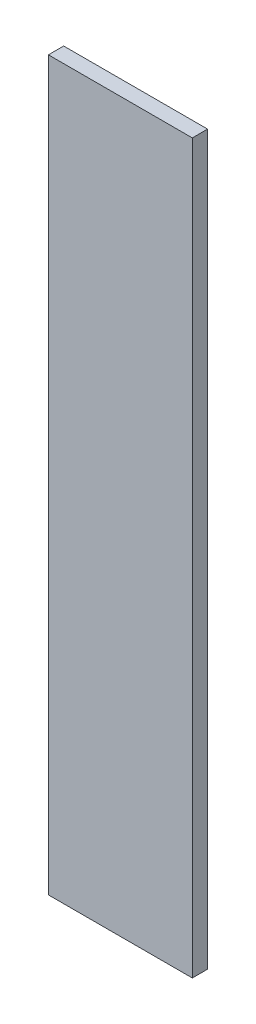
SolidWorks part; units mm, degrees
ref_plane "Front Plane" through (0, 0, 0) normal (0, 0, 1) x (1, 0, 0)
ref_plane "Top Plane" through (0, 0, 0) normal (0, 1, 0) x (1, 0, 0)
ref_plane "Right Plane" through (0, 0, 0) normal (1, 0, 0) x (0, 0, -1)
sketch "Sketch1" plane through (0, 0, 0) normal (0, 0, 1) x (1, 0, 0)
  line L0 (-100.4665, 0) -> (-100.4665, 140)
  line L1 (-100.4665, 140) -> (-100.4665, 143)
  line L2 (-100.4665, 143) -> (-72.1822, 143)
  line L3 (-72.1822, 143) -> (-72.1822, 0)
  line L4 (-72.1822, 0) -> (-100.4665, 0)
extrude "Boss-Extrude1" add sketch "Sketch1" along normal blind 3
